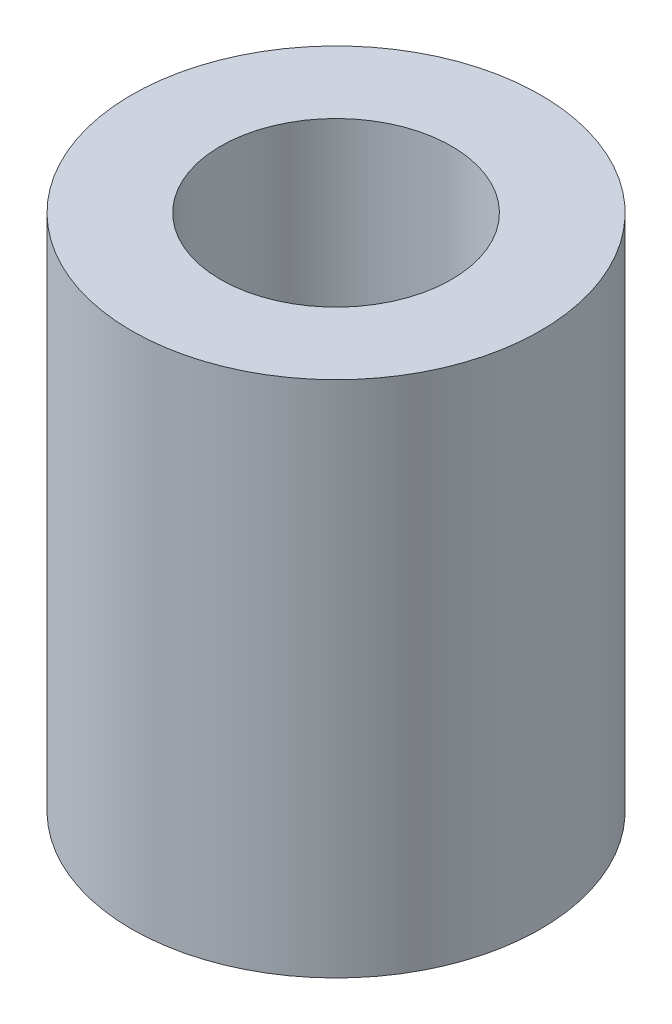
SolidWorks part; units mm, degrees
material "Nylon 101"
ref_plane "Front Plane" through (0, 0, 0) normal (0, 0, 1) x (1, 0, 0)
ref_plane "Top Plane" through (0, 0, 0) normal (0, 1, 0) x (1, 0, 0)
ref_plane "Right Plane" through (0, 0, 0) normal (1, 0, 0) x (0, 0, -1)
sketch "Sketch1" plane through (0, 0, 0) normal (0, 1, 0) x (1, 0, 0)
  circle A0 centre (0, 0) radius 5.842
  circle A1 centre (0, 0) radius 3.302
  dimension "D1" = 6.604
  dimension "D2" = 11.684
extrude "Boss-Extrude1" add sketch "Sketch1" along normal blind 14.8082
